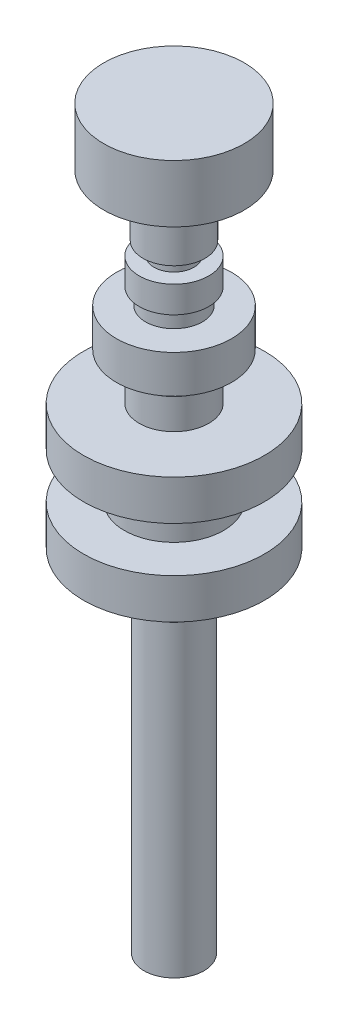
SolidWorks part; units mm, degrees
ref_plane "Front Plane" through (0, 0, 0) normal (0, 0, 1) x (1, 0, 0)
ref_plane "Top Plane" through (0, 0, 0) normal (0, 1, 0) x (1, 0, 0)
ref_plane "Right Plane" through (0, 0, 0) normal (1, 0, 0) x (0, 0, -1)
sketch "Sketch1" plane through (0, 0, 0) normal (0, 0, 1) x (1, 0, 0)
  line L0 (0, 0) -> (0, 116.45) construction
  line L1 (0, 0) -> (4.75, 0)
  line L2 (4.75, 0) -> (4.75, 49.8)
  line L3 (4.75, 49.8) -> (6.3, 49.8)
  line L4 (6.3, 49.8) -> (6.3, 55.5)
  line L5 (6.3, 55.5) -> (14.3, 55.5)
  line L6 (14.3, 55.5) -> (14.3, 61.85)
  line L7 (14.3, 61.85) -> (7.85, 61.85)
  line L8 (7.85, 61.85) -> (7.85, 69)
  line L9 (7.85, 69) -> (14.3, 69)
  line L10 (14.3, 69) -> (14.3, 75.35)
  line L11 (14.3, 75.35) -> (5.5, 75.35)
  line L12 (5.5, 75.35) -> (5.5, 80.15)
  line L13 (5.5, 80.15) -> (4.5, 80.15)
  line L14 (4.5, 80.15) -> (4.5, 82.75)
  line L15 (4.5, 82.75) -> (9.1, 82.75)
  line L16 (9.1, 82.75) -> (9.1, 88.75)
  line L17 (9.1, 88.75) -> (4.5, 88.75)
  line L18 (4.5, 88.75) -> (4.5, 91.35)
  line L19 (4.5, 91.35) -> (5.5, 91.35)
  line L20 (5.5, 91.35) -> (5.5, 95.55)
  line L21 (5.5, 95.55) -> (3.15, 95.55)
  line L22 (3.15, 95.55) -> (3.15, 97.65)
  line L23 (3.15, 97.65) -> (4.9, 97.65)
  line L24 (4.9, 97.65) -> (4.9, 107.35)
  line L25 (4.9, 107.35) -> (11.1, 107.35)
  line L26 (11.1, 107.35) -> (11.1, 116.45)
  line L27 (11.1, 116.45) -> (0, 116.45)
  line L28 (0, 0) -> (0, 116.45) construction
  line L29 (0, 0) -> (0, 116.45)
  point P30 (4.9, 102.5)
  dimension "D1" = 49.8
  dimension "D2" = 5.7
  dimension "D3" = 6.35
  dimension "D4" = 7.15
  dimension "D5" = 6.35
  dimension "D6" = 4.8
  dimension "D7" = 2.6
  dimension "D8" = 6
  dimension "D9" = 2.6
  dimension "D10" = 4.2
  dimension "D11" = 2.1
  dimension "D12" = 9.7
  dimension "D13" = 9.1
  dimension "D14" = 22.2
  dimension "D15" = 9.8
  dimension "D16" = 6.3
  dimension "D17" = 11
  dimension "D18" = 9.5
  dimension "D19" = 12.6
  dimension "D20" = 28.6
  dimension "D21" = 15.7
  dimension "D22" = 11
  dimension "D23" = 9
  dimension "D24" = 18.2
  dimension "D25" = 9
revolve "Revolve2" add sketch "Sketch1" angle 360 about L29
